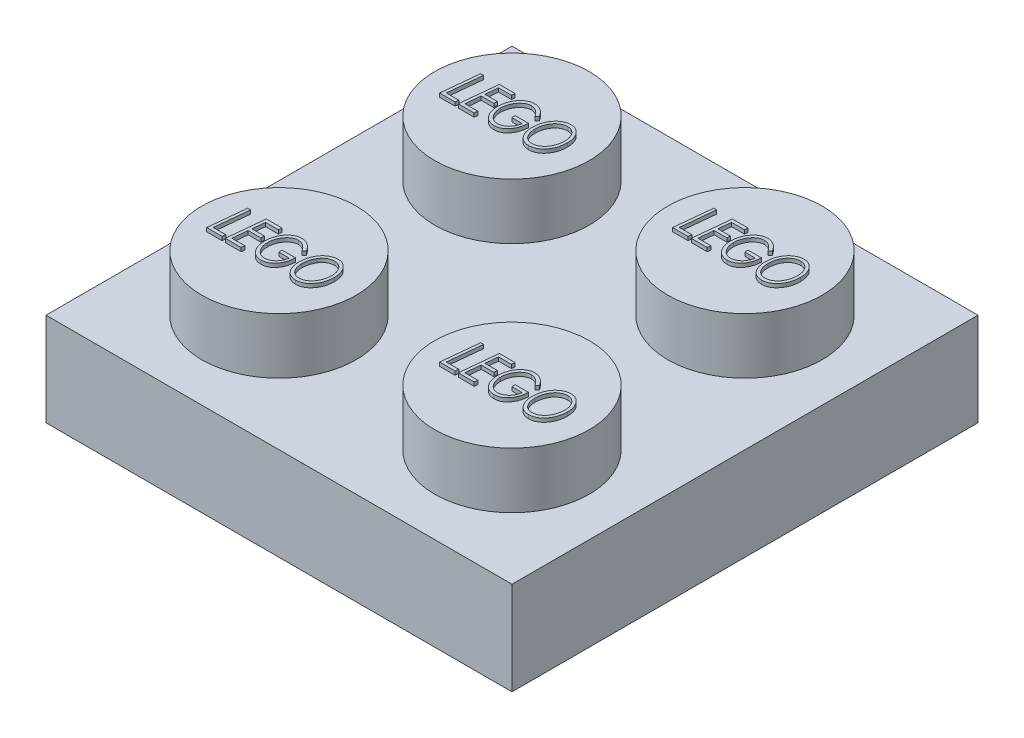
SolidWorks part; units mm, degrees
ref_plane "Front Plane" through (0, 0, 0) normal (0, 0, 1) x (1, 0, 0)
ref_plane "Top Plane" through (0, 0, 0) normal (0, 1, 0) x (1, 0, 0)
ref_plane "Right Plane" through (0, 0, 0) normal (1, 0, 0) x (0, 0, -1)
sketch "Sketch2" plane through (0, 0, 0) normal (0, 1, 0) x (1, 0, 0)
  line L0 (-17.7331, 8.7234) -> (-1.8581, 8.7234)
  line L1 (-1.8581, 8.7234) -> (-1.8581, -7.1516)
  line L2 (-1.8581, -7.1516) -> (-17.7331, -7.1516)
  line L3 (-17.7331, -7.1516) -> (-17.7331, 8.7234)
  dimension "D1" = 15.875
  dimension "D2" = 15.875
extrude "Boss-Extrude3" add sketch "Sketch2" along normal blind 3.175
sketch "Sketch3" plane through (0, 3.175, 0) normal (0, 1, 0) x (1, 0, 0)
  line L0 (-17.7331, 8.7234) -> (-17.7331, -7.1516) construction
  line L1 (-1.8581, 8.7234) -> (-17.7331, 8.7234) construction
  circle A0 centre (-13.7644, 4.7546) radius 2.6308
  dimension "D1" = 3.9687
  dimension "D2" = 3.9688
extrude "Boss-Extrude4" add sketch "Sketch3" along normal blind 1.905
pattern_linear "LPattern1" count 2 spacing 7.9375 along (1, 0, 0) count 2 spacing 7.9375 along (0, 0, 1) of "Boss-Extrude4"
shell "Shell1" thickness 1.524
sketch "Sketch4" plane through (0, 5.08, 0) normal (0, 1, 0) x (1, 0, 0)
  line L1 (-13.7644, 4.7546) -> (-13.7644, 4.0766) construction
  line L2 (-15.584, 4.0766) -> (-11.9447, 4.0766) construction
  text T0 "<i>LEGO</i>" font "Century Gothic" height 1.27
  point P4 (-13.7644, 4.7546)
  point P9 (-13.7644, 4.0766)
extrude "Boss-Extrude5" add sketch "Sketch4" along normal blind 0.127
pattern_linear "LPattern2" count 2 spacing 7.9375 along (1, 0, 0) count 2 spacing 7.9375 along (0, 0, 1) of "Boss-Extrude5"
sketch "Sketch5" plane through (0, 0, 0) normal (0, -1, 0) x (1, 0, 0)
  circle A2 centre (-9.7956, -0.7859) radius 3.175
  circle A3 centre (-9.7956, -0.7859) radius 2.3876
  dimension "D1" = 6.35
  dimension "D2" = 4.7752
extrude "Boss-Extrude6" add sketch "Sketch5" against normal up to surface (1.651 mm away) up to face at (-5.8269, 1.651, -5.8614)
